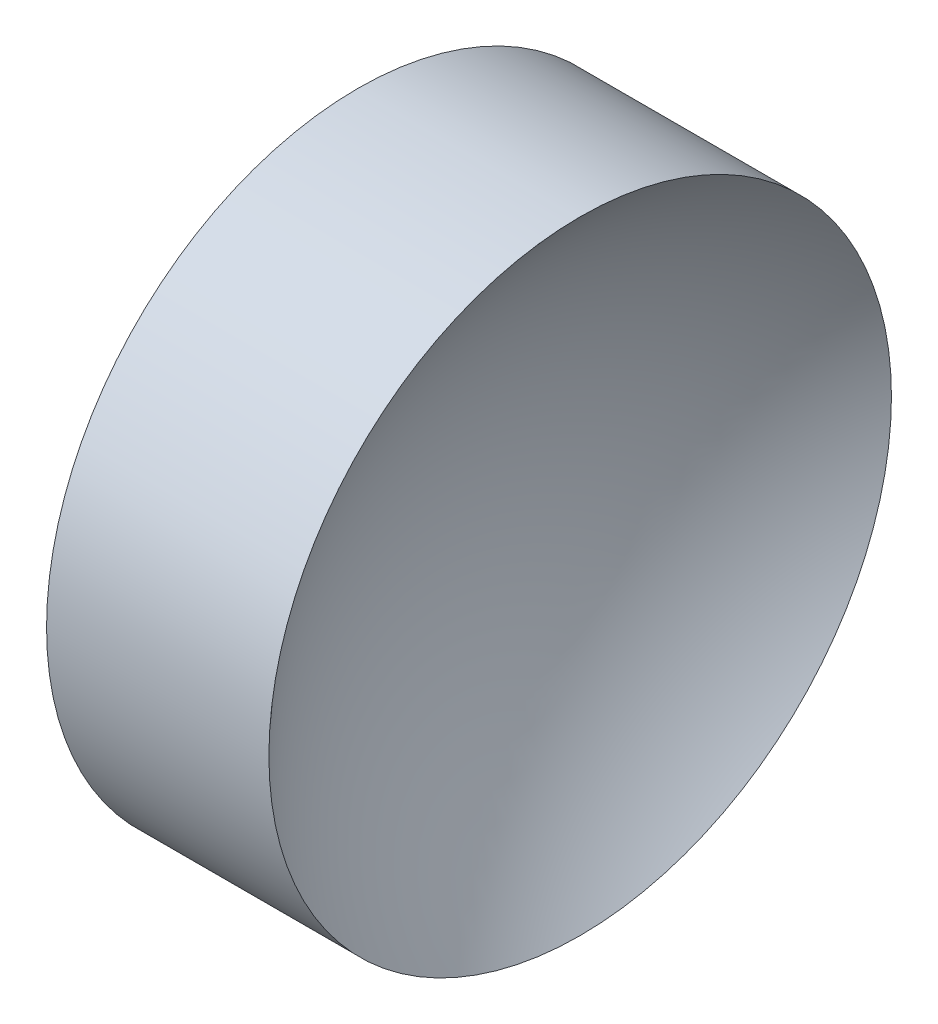
SolidWorks part; units mm, degrees
ref_plane "前视基准面" through (0, 0, 0) normal (0, 0, 1) x (1, 0, 0)
ref_plane "上视基准面" through (0, 0, 0) normal (0, 1, 0) x (1, 0, 0)
ref_plane "右视基准面" through (0, 0, 0) normal (1, 0, 0) x (0, 0, -1)
sketch "草图1" plane through (0, 0, 0) normal (0, 0, 1) x (1, 0, 0)
  line L0 (21.1565, 13.0311) -> (26.8361, 13.0311) construction
  line L1 (22.2009, 13.0311) -> (22.2009, 16.1811)
  line L2 (22.2009, 16.1811) -> (24.4509, 16.1811)
  line L3 (23.2009, 13.0311) -> (22.2009, 13.0311)
  arc A0 (24.4509, 16.1811) -> (23.2009, 13.0311) centre (27.7949, 13.0311) ccw
revolve "旋转1" add sketch "草图1" angle 360 about L0
